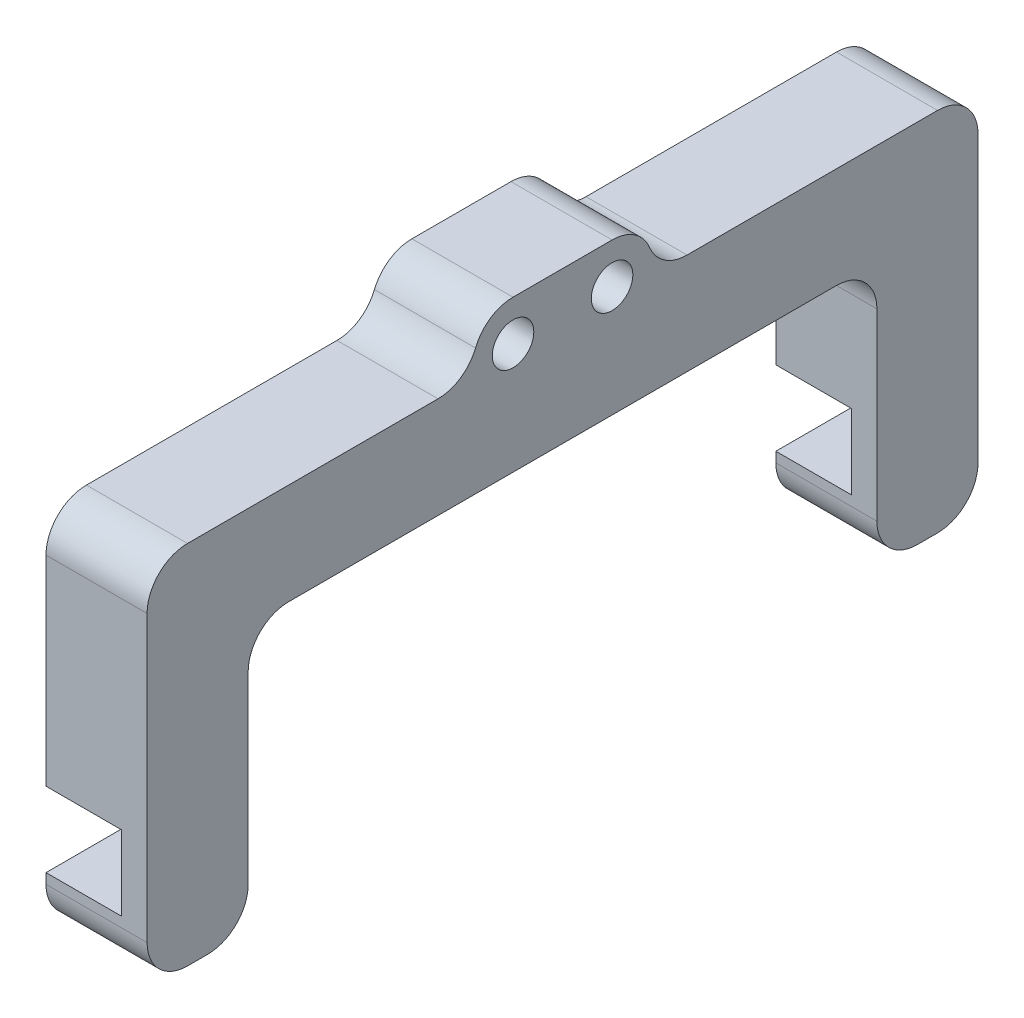
SolidWorks part; units mm, degrees
ref_plane "Front Plane" through (0, 0, 0) normal (0, 0, 1) x (1, 0, 0)
ref_plane "Top Plane" through (0, 0, 0) normal (0, 1, 0) x (1, 0, 0)
ref_plane "Right Plane" through (0, 0, 0) normal (1, 0, 0) x (0, 0, -1)
sketch "Sketch1" plane through (0, 0, 0) normal (1, 0, 0) x (0, 0, -1)
  line L0 (17.8, -5) -> (50, -5)
  line L1 (0, 0) -> (17.8, 0)
  line L4 (17.8, 0) -> (17.8, -5)
  line L9 (-32.2, -15) -> (50, -15)
  line L10 (50, -15) -> (50, -5)
  line L11 (0, 0) -> (0, -5)
  line L12 (0, -5) -> (-32.2, -5)
  line L13 (-32.2, -5) -> (-32.2, -15)
  dimension "D1" = 17.8
  dimension "D2" = 5
  dimension "D3" = 10
  dimension "D4" = 32.2
extrude "Boss-Extrude1" add sketch "Sketch1" along normal blind 10
sketch "Sketch3" plane through (10, 0, 0) normal (1, 0, 0) x (0, 0, -1)
  line L0 (0, -4) -> (17.8, -4) construction
  line L2 (17.8, -5) -> (17.8, 0) construction
  line L3 (17.8, 0) -> (0, 0) construction
  line L4 (0, 0) -> (0, -5) construction
  circle A0 centre (4, -4) radius 2.055
  circle A1 centre (13.8, -4) radius 2.055
  dimension "D4" = 4.11
  dimension "D1" = 4
  dimension "D2" = 4
  dimension "D3" = 4
extrude "Cut-Extrude1" cut sketch "Sketch3" against normal through all
sketch "Sketch5" plane through (10, 0, 0) normal (1, 0, 0) x (0, 0, -1)
  line L0 (-32.2, -15) -> (50, -15) construction
  line L1 (-32.2, -15) -> (-22.2, -15)
  line L2 (-32.2, -15) -> (-32.2, -28.8)
  line L3 (-32.2, -28.8) -> (-22.2, -28.8)
  line L4 (-22.2, -15) -> (-22.2, -28.8)
  line L5 (40, -15) -> (50, -15)
  line L6 (40, -15) -> (40, -28.8)
  line L7 (40, -28.8) -> (50, -28.8)
  line L8 (50, -15) -> (50, -28.8)
  dimension "D1" = 10
  dimension "D2" = 13.8
extrude "Boss-Extrude2" add sketch "Sketch5" against normal up to surface (10 mm away) up to face at (0, -4, -6.055)
sketch "Sketch10" plane through (10, 0, 0) normal (1, 0, 0) x (0, 0, -1)
  line L1 (-32.2, -28.8) -> (-22.2, -28.8)
  line L2 (-32.2, -28.8) -> (-32.2, -36.2)
  line L3 (-32.2, -36.2) -> (-22.2, -36.2)
  line L4 (-22.2, -28.8) -> (-22.2, -36.2)
  point P5 (-22.2, -28.9)
  dimension "D1" = 7.4
extrude "Boss-Extrude5" add sketch "Sketch10" against normal blind 2.5289
sketch "Sketch11" plane through (10, 0, 0) normal (1, 0, 0) x (0, 0, -1)
  line L1 (-32.2, -36.2) -> (-22.2, -36.2)
  line L2 (-32.2, -36.2) -> (-32.2, -41.2)
  line L3 (-32.2, -41.2) -> (-22.2, -41.2)
  line L4 (-22.2, -36.2) -> (-22.2, -41.2)
  point P5 (-22.2, -36.2)
  dimension "D1" = 5
extrude "Boss-Extrude6" add sketch "Sketch11" against normal up to surface (10 mm away) up to face at (0, -4, -6.055)
ref_plane "Plane1" through (0, 0, -8.9) normal (0, 0, 1) x (1, 0, 0)
mirror "Mirror1" about plane through (0, 0, -8.9) normal (0, 0, 1) of "Boss-Extrude5", "Boss-Extrude6"
fillet "Fillet1" radius 4 2 edges at (5, 0, -17.8) (5, 0, 0)
fillet "Fillet2" radius 4 8 edges at (5, -41.2, -50) (5, -41.2, -40) (5, -15, -40) (5, -15, 22.2) (5, -41.2, 22.2) (5, -41.2, 32.2) (5, -5, -50) (5, -5, 32.2)
fillet "Fillet3" radius 4 2 edges at (5, -5, -17.8) (5, -5, 0)
